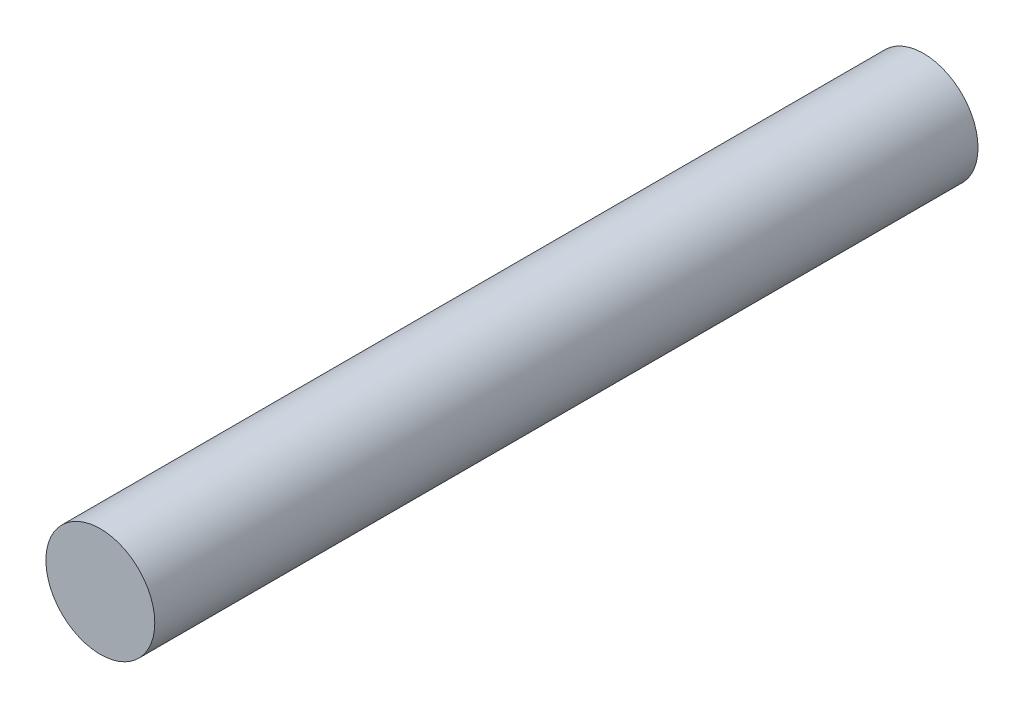
SolidWorks part; units mm, degrees
ref_plane "Front Plane" through (0, 0, 0) normal (0, 0, 1) x (1, 0, 0)
ref_plane "Top Plane" through (0, 0, 0) normal (0, 1, 0) x (1, 0, 0)
ref_plane "Right Plane" through (0, 0, 0) normal (1, 0, 0) x (0, 0, -1)
sketch "Sketch1" plane through (0, 0, 0) normal (0, 0, 1) x (1, 0, 0)
  circle A0 centre (0, 0) radius 1.5
  dimension "D1" = 3
extrude "Boss-Extrude1" add sketch "Sketch1" along normal blind 22.68
